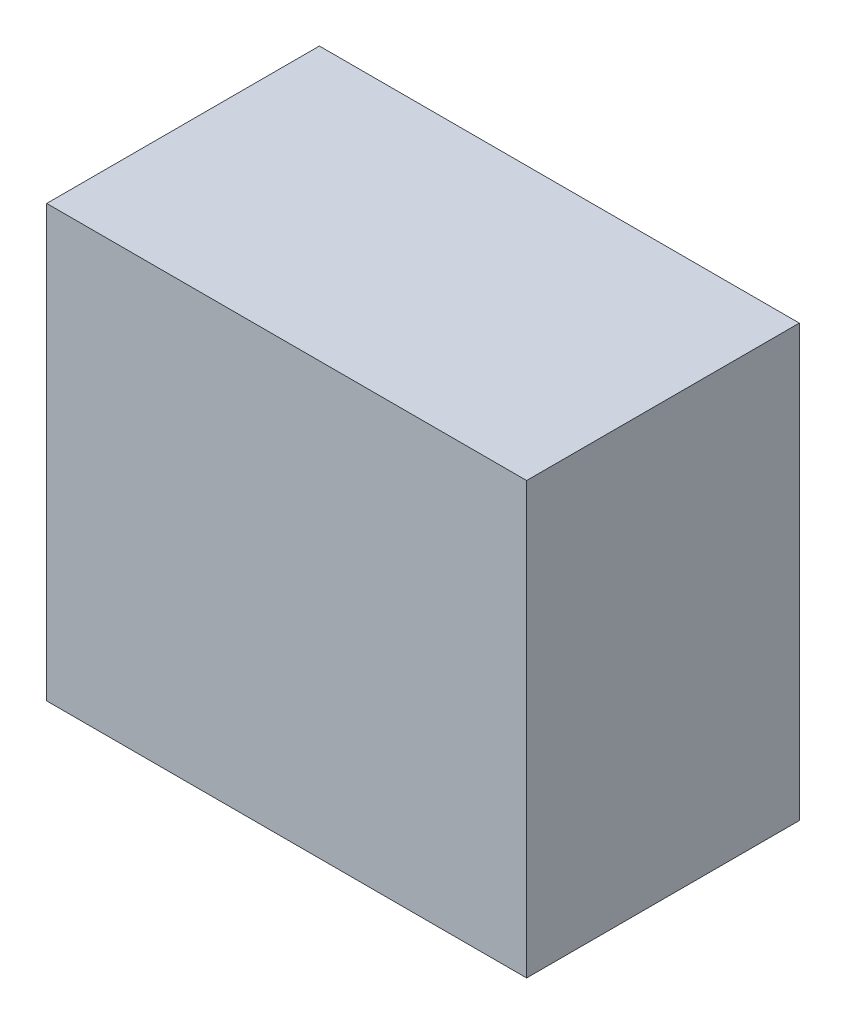
SolidWorks part; units mm, degrees
ref_plane "Front Plane" through (0, 0, 0) normal (0, 0, 1) x (1, 0, 0)
ref_plane "Top Plane" through (0, 0, 0) normal (0, 1, 0) x (1, 0, 0)
ref_plane "Right Plane" through (0, 0, 0) normal (1, 0, 0) x (0, 0, -1)
sketch "Sketch1" plane through (0, 0, 0) normal (0, 0, 1) x (1, 0, 0)
  line L1 (-11.176, -10.033) -> (11.176, -10.033)
  line L2 (-11.176, -10.033) -> (-11.176, 10.033)
  line L3 (-11.176, 10.033) -> (11.176, 10.033)
  line L4 (11.176, -10.033) -> (11.176, 10.033)
  line L5 (-11.176, -10.033) -> (11.176, 10.033) construction
  line L6 (-11.176, 10.033) -> (11.176, -10.033) construction
  point P0 (0, 0)
  dimension "D1" = 22.352
  dimension "D2" = 20.066
extrude "Extrude1" add sketch "Sketch1" along normal mid plane 12.7
sketch "Sketch2" plane through (0, -10.033, 0) normal (0, -1, 0) x (1, 0, 0)
  line L0 (-11.176, 6.35) -> (11.176, -6.35) construction
  circle A0 centre (0, 0) radius 2.3813
  dimension "D1" = 4.7625
extrude "Extrude2" cut sketch "Sketch2" against normal blind 12.7
sketch "Sketch3" plane through (11.176, 0, 0) normal (1, 0, 0) x (0, 0, -1)
  line L0 (-6.35, 10.033) -> (-6.35, -10.033)
  line L1 (-6.35, -10.033) -> (-5.6493, 10.033)
  line L2 (-6.35, 10.033) -> (6.35, 10.033) construction
  line L3 (-5.6493, 10.033) -> (-6.35, 10.033)
  line L4 (0, 10.033) -> (0, -10.033) construction
  line L5 (-6.35, -10.033) -> (6.35, -10.033) construction
  line L6 (5.6493, 10.033) -> (6.35, 10.033)
  line L7 (6.35, -10.033) -> (5.6493, 10.033)
  line L8 (6.35, 10.033) -> (6.35, -10.033)
  dimension "D1" = 2
extrude "Extrude3" [suppressed] cut sketch "Sketch3" against normal through all
